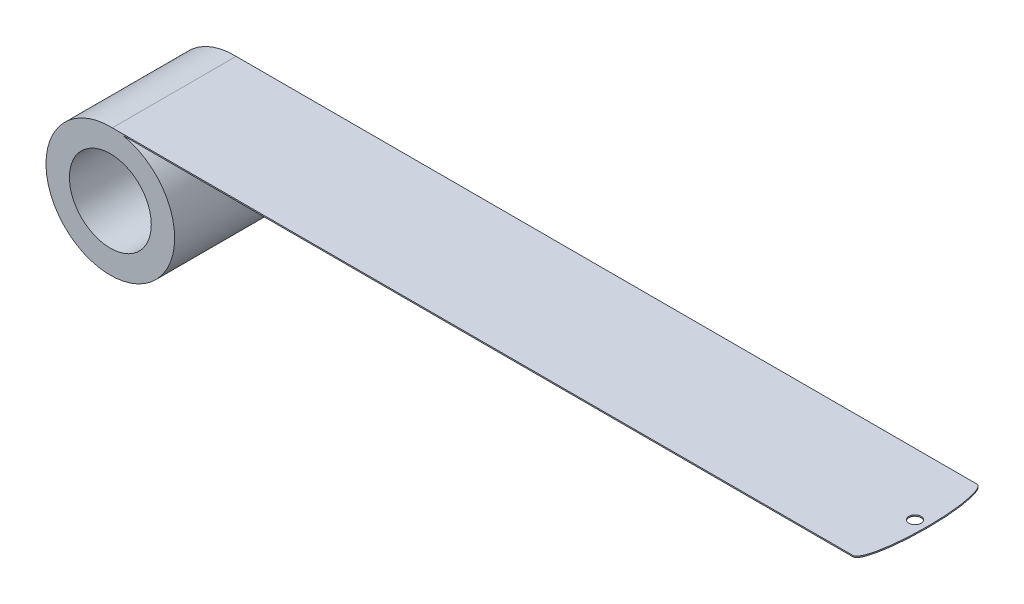
SolidWorks part; units mm, degrees
ref_plane "Front Plane" through (0, 0, 0) normal (0, 0, 1) x (1, 0, 0)
ref_plane "Top Plane" through (0, 0, 0) normal (0, 1, 0) x (1, 0, 0)
ref_plane "Right Plane" through (0, 0, 0) normal (1, 0, 0) x (0, 0, -1)
sketch "Sketch1" plane through (0, 0, 0) normal (0, 0, 1) x (1, 0, 0)
  circle A0 centre (0, 0) radius 26.4033
  circle A1 centre (0, 0) radius 16.8021
  dimension "D1" = 52.8066
  dimension "D2" = 33.6042
extrude "Boss-Extrude1" add sketch "Sketch1" along normal blind 50.8
ref_plane "Plane1" through (0, 25.8826, 0) normal (0, 1, 0) x (1, 0, 0)
sketch "Sketch2" plane through (0, 25.8826, 0) normal (0, 1, 0) x (1, 0, 0)
  line L0 (-26.4033, -50.8) -> (26.4033, -50.8) construction
  line L1 (-26.4033, -50.8) -> (26.4033, -50.8) construction
  line L2 (26.4033, 0) -> (-26.4033, 0) construction
  line L3 (26.4033, 0) -> (-26.4033, 0) construction
  line L4 (0, -50.8) -> (0, 0)
  line L5 (0, 0) -> (304.8, 0)
  line L6 (0, -50.8) -> (304.8, -50.8)
  circle A0 centre (304.8, -25.4) radius 2.4892
  ellipse E0 centre (304.8, -25.4) end of major axis (304.8, 0) minor radius 4.9608 (304.8, -50.8) -> (304.8, 0) ccw
  dimension "D1" = 4.9784
  dimension "D2" = 304.8
extrude "Boss-Extrude2" add sketch "Sketch2" along normal blind 0.508
